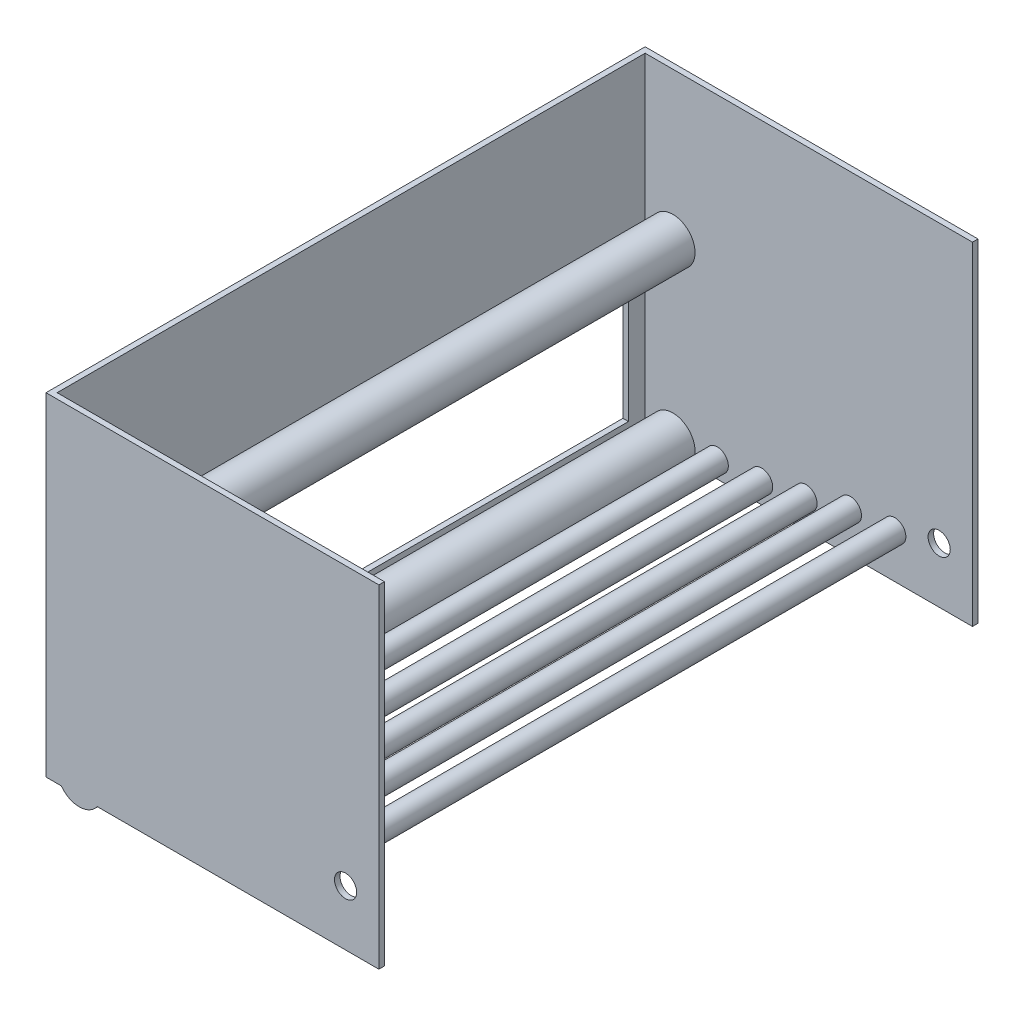
SolidWorks part; units mm, degrees
ref_plane "Front Plane" through (0, 0, 0) normal (0, 0, 1) x (1, 0, 0)
ref_plane "Top Plane" through (0, 0, 0) normal (0, 1, 0) x (1, 0, 0)
ref_plane "Right Plane" through (0, 0, 0) normal (1, 0, 0) x (0, 0, -1)
sketch "Sketch1" plane through (0, 0, 0) normal (0, 1, 0) x (1, 0, 0)
  line L1 (0, 0) -> (381, 0)
  line L2 (0, 0) -> (0, 685.8)
  line L3 (0, 685.8) -> (381, 685.8)
  line L4 (381, 0) -> (381, 685.8)
  dimension "D1" = 381
  dimension "D2" = 685.8
extrude "Boss-Extrude1" add sketch "Sketch1" along normal blind 381
shell "Shell1" thickness 6.35
sketch "Sketch4" plane through (0, 0, 0) normal (0, 0, 1) x (1, 0, 0)
  line L0 (381, 381) -> (381, 0) construction
  line L1 (0, 0) -> (381, 0) construction
  circle A0 centre (342.9, 63.5) radius 12.7
  dimension "D1" = 38.1
  dimension "D2" = 25.4
  dimension "D3" = 63.5
extrude "Cut-Extrude1" cut sketch "Sketch4" against normal through all both and the other way through all
sketch "Sketch5" plane through (0, 0, 0) normal (0, 0, 1) x (1, 0, 0)
  line L0 (292.1, 50.8) -> (241.3, 46.3556) construction
  line L1 (241.3, 46.3556) -> (190.5, 32.7438) construction
  line L2 (190.5, 32.7438) -> (139.7, 23.7863) construction
  line L3 (139.7, 23.7863) -> (88.9, 19.3419) construction
  line L4 (88.9, 19.3419) -> (38.1, 14.8975) construction
  line L5 (292.1, 50.8) -> (342.9, 50.8) construction
  line L7 (292.1, 50.8) -> (342.9, 50.8) construction
  circle A0 centre (292.1, 50.8) radius 12.7
  circle A2 centre (190.5, 32.7438) radius 12.7
  circle A3 centre (88.9, 19.3419) radius 12.7
  circle A4 centre (241.3, 46.3556) radius 12.7
  circle A5 centre (139.7, 23.7863) radius 12.7
  circle A6 centre (342.9, 63.5) radius 12.7 construction
  circle A7 centre (342.9, 63.5) radius 12.7 construction
  circle A8 centre (38.1, 14.8975) radius 25.4 construction
  dimension "D1" = 25.4
  dimension "D7" = 50.8
  dimension "D9" = 190
  dimension "D11" = 175
  dimension "D2" = 50.8
  dimension "D3" = 50.8
  dimension "D4" = 50.8
  dimension "D5" = 50.8
  dimension "D6" = 12.7
  dimension "D8" = 50.8
  dimension "D10" = 175
  dimension "D12" = 180
  dimension "D13" = 50.8
  dimension "D14" = 175
extrude "Boss-Extrude3" add sketch "Sketch5" against normal up to surface (679.45 mm away) up to face at (355.6, 63.5, -679.45)
sketch "Sketch6" plane through (0, 0, 0) normal (0, 0, 1) x (1, 0, 0)
  circle A0 centre (38.1, 14.8975) radius 25.4
  circle A1 centre (38.1, 211.7475) radius 25.4
  point P5 (0, 0)
  dimension "D1" = 50.8
  dimension "D2" = 146.05
extrude "Boss-Extrude4" add sketch "Sketch6" against normal up to surface (679.45 mm away) up to face at (152.4, 23.7863, -679.45)
sketch "Sketch7" plane through (6.35, 0, 0) normal (1, 0, 0) x (0, 0, -1)
  line L0 (0, 381) -> (0, 0) construction
  line L1 (25.4, 190.5) -> (660.4, 190.5)
  line L2 (25.4, 190.5) -> (25.4, 25.4)
  line L3 (25.4, 25.4) -> (660.4, 25.4)
  line L4 (660.4, 190.5) -> (660.4, 25.4)
  line L5 (685.8, 381) -> (685.8, 0) construction
  line L6 (685.8, 0) -> (0, 0) construction
  dimension "D1" = 25.4
  dimension "D2" = 25.4
  dimension "D3" = 25.4
  dimension "D4" = 165.1
extrude "Cut-Extrude3" cut sketch "Sketch7" against normal up to next
